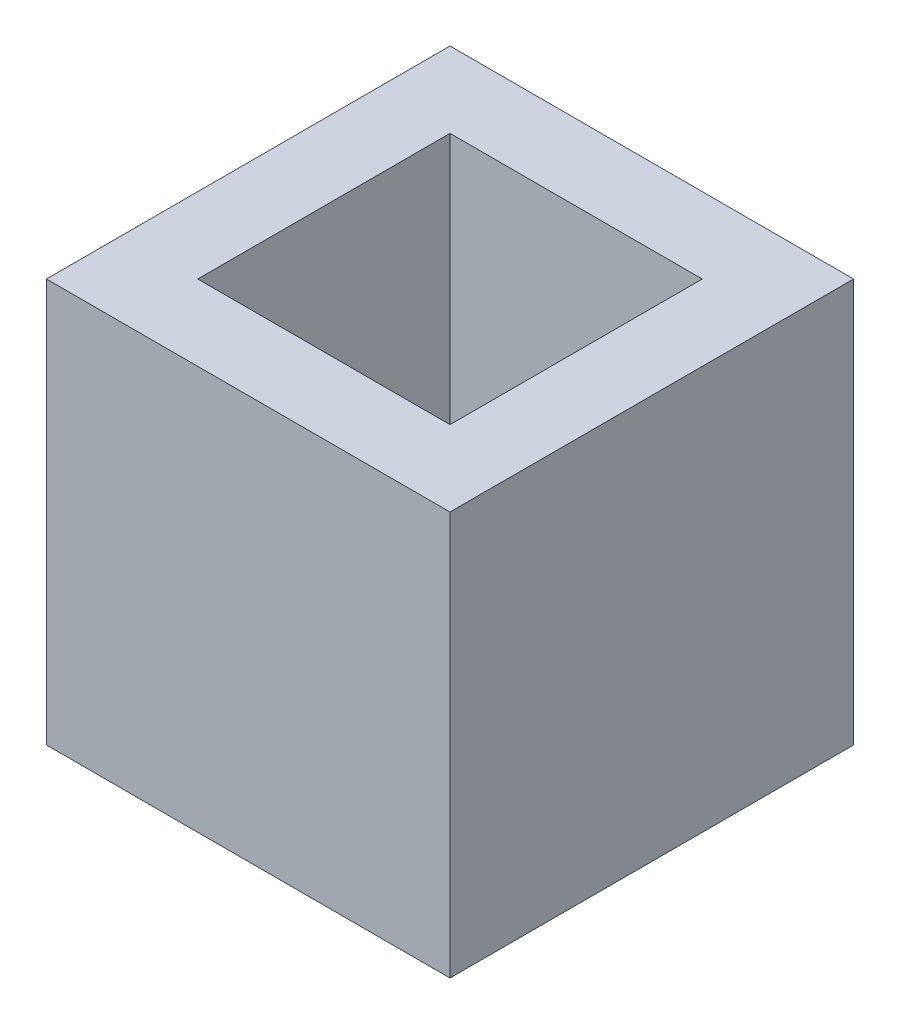
SolidWorks part; units mm, degrees
ref_plane "Front Plane" through (0, 0, 0) normal (0, 0, 1) x (1, 0, 0)
ref_plane "Top Plane" through (0, 0, 0) normal (0, 1, 0) x (1, 0, 0)
ref_plane "Right Plane" through (0, 0, 0) normal (1, 0, 0) x (0, 0, -1)
sketch "Sketch1" plane through (0, 0, 0) normal (0, 1, 0) x (1, 0, 0)
  line L1 (0, 0) -> (25.4, 0)
  line L2 (0, 0) -> (0, 25.4)
  line L3 (0, 25.4) -> (25.4, 25.4)
  line L4 (25.4, 0) -> (25.4, 25.4)
  dimension "D1" = 25.4
  dimension "D2" = 25.4
extrude "Boss-Extrude1" add sketch "Sketch1" along normal blind 25.4
sketch "Sketch2" plane through (0, 25.4, 0) normal (0, 1, 0) x (1, 0, 0)
  line L0 (25.4, 0) -> (25.4, 25.4) construction
  line L1 (4.7625, 4.7625) -> (20.6375, 4.7625)
  line L2 (4.7625, 4.7625) -> (4.7625, 20.6375)
  line L3 (4.7625, 20.6375) -> (20.6375, 20.6375)
  line L4 (20.6375, 4.7625) -> (20.6375, 20.6375)
  line L5 (4.7625, 4.7625) -> (20.6375, 20.6375) construction
  line L6 (4.7625, 20.6375) -> (20.6375, 4.7625) construction
  line L7 (25.4, 25.4) -> (0, 25.4) construction
  point P0 (12.7, 12.7)
  point P7 (25.4, 12.7)
  point P10 (12.7, 25.4)
  dimension "D1" = 15.875
  dimension "D2" = 15.875
extrude "Cut-Extrude1" cut sketch "Sketch2" against normal through all
